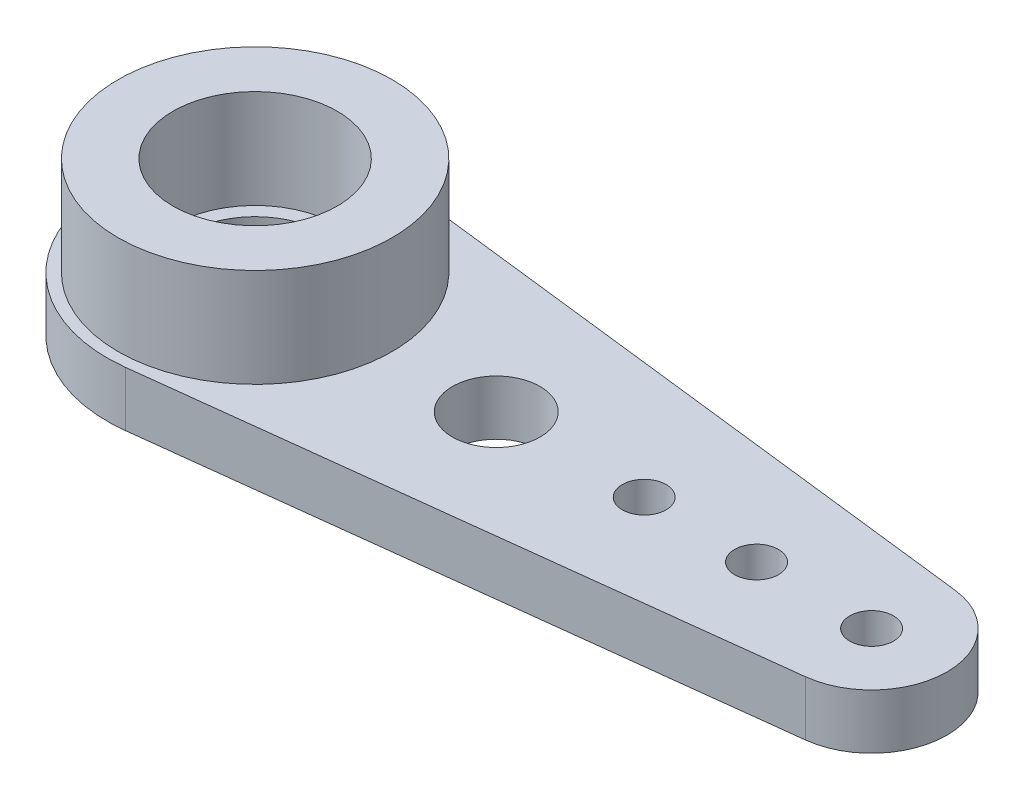
SolidWorks part; units mm, degrees
ref_plane "前基準面" through (0, 0, 0) normal (0, 0, 1) x (1, 0, 0)
ref_plane "上基準面" through (0, 0, 0) normal (0, 1, 0) x (1, 0, 0)
ref_plane "右基準面" through (0, 0, 0) normal (1, 0, 0) x (0, 0, -1)
sketch "草圖1" plane through (0, 0, 0) normal (0, 1, 0) x (1, 0, 0)
  line L0 (0.636, 5.3624) -> (22.8239, 2.7309)
  line L1 (0, 0) -> (0, 21.3437) construction
  line L2 (0, 0) -> (22.5, 0) construction
  line L3 (22.8239, -2.7309) -> (0.636, -5.3624)
  circle A0 centre (0, 0) radius 2.5
  arc A1 (0.636, 5.3624) -> (0.636, -5.3624) centre (0, 0) ccw
  circle A2 centre (8.8, 0) radius 1.6
  circle A3 centre (14.2, 0) radius 0.8
  circle A4 centre (18.3, 0) radius 0.8
  arc A5 (22.8239, -2.7309) -> (22.8239, 2.7309) centre (22.5, 0) ccw
  circle A6 centre (22.5, 0) radius 0.8
  dimension "D1" = 5
  dimension "D2" = 10.8
  dimension "D3" = 8.8
  dimension "D4" = 14.2
  dimension "D5" = 18.3
  dimension "D6" = 22.5
  dimension "D7" = 5.5
  dimension "D8" = 3.2
  dimension "D9" = 1.6
  dimension "D10" = 1.6
  dimension "D11" = 1.6
extrude "伸長1" add sketch "草圖1" along normal blind 2
sketch "草圖4" plane through (0, 2, 0) normal (0, 1, 0) x (1, 0, 0)
  circle A0 centre (0, 0) radius 5
  circle A1 centre (0, 0) radius 3
  dimension "D1" = 10
  dimension "D2" = 6
extrude "填料-伸長1" add sketch "草圖4" along normal blind 3.6
